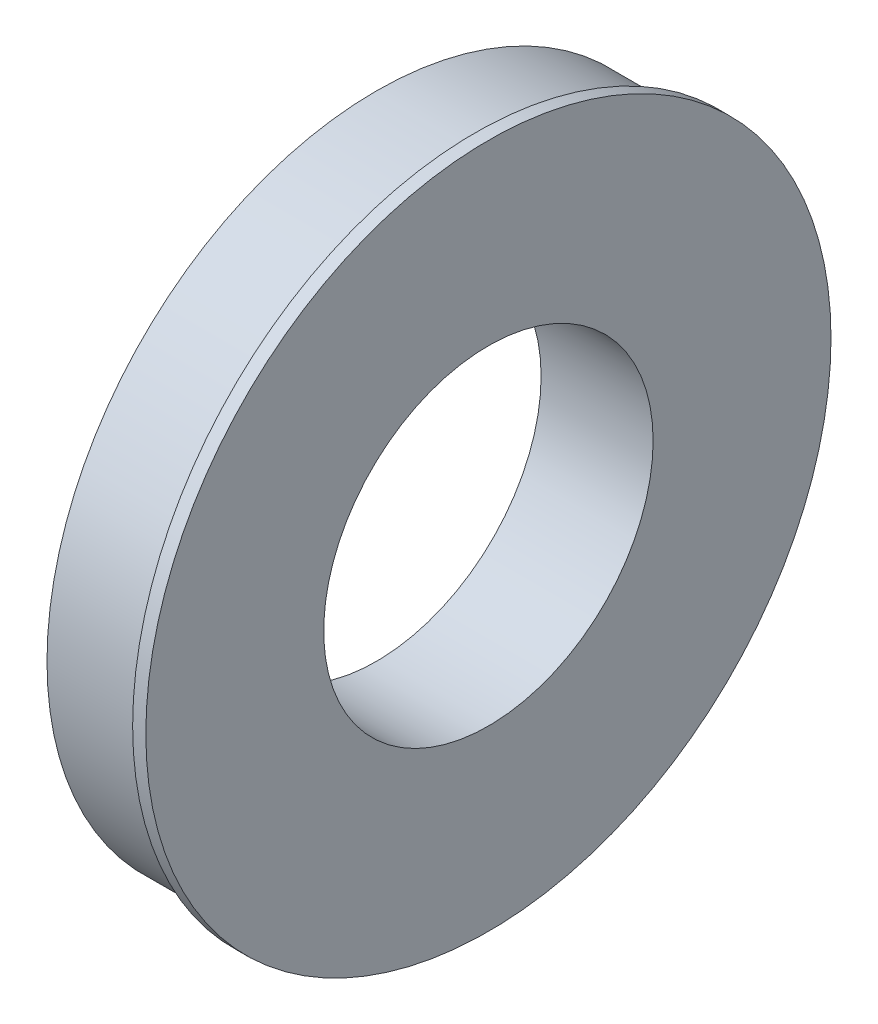
SolidWorks part; units mm, degrees
ref_plane "Alzado" through (0, 0, 0) normal (0, 0, 1) x (1, 0, 0)
ref_plane "Planta" through (0, 0, 0) normal (0, 1, 0) x (1, 0, 0)
ref_plane "Vista lateral" through (0, 0, 0) normal (1, 0, 0) x (0, 0, -1)
sketch "Croquis1" plane through (0, 0, 0) normal (1, 0, 0) x (0, 0, -1)
  circle A0 centre (0, 0) radius 31.75
  circle A1 centre (0, 0) radius 63.5
  dimension "D1" = 127
  dimension "D2" = 63.5
extrude "Saliente-Extruir1" add sketch "Croquis1" along normal blind 19.05
sketch "Croquis2" plane through (19.05, 0, 0) normal (1, 0, 0) x (0, 0, -1)
  circle A4 centre (0, 0) radius 31.75 construction
  circle A5 centre (0, 0) radius 31.75
  circle A8 centre (0, 0) radius 66.04
  circle A9 centre (0, 0) radius 66.04
  dimension "D1" = 2.54
extrude "Saliente-Extruir3" add sketch "Croquis2" along normal blind 2.54
